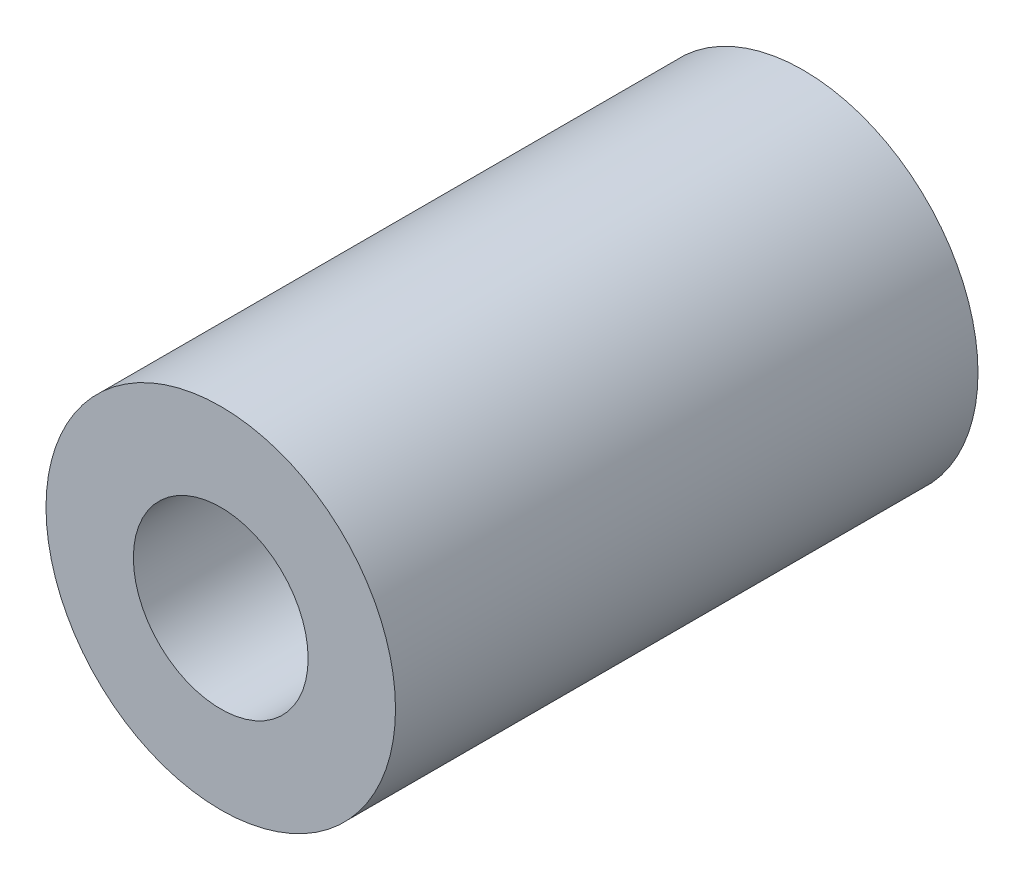
SolidWorks part; units mm, degrees
material "1060 Alloy"
ref_plane "Front Plane" through (0, 0, 0) normal (0, 0, 1) x (1, 0, 0)
ref_plane "Top Plane" through (0, 0, 0) normal (0, 1, 0) x (1, 0, 0)
ref_plane "Right Plane" through (0, 0, 0) normal (1, 0, 0) x (0, 0, -1)
sketch "Sketch1" plane through (0, 0, 0) normal (0, 0, 1) x (1, 0, 0)
  circle A0 centre (0, 0) radius 1.5
  circle A1 centre (0, 0) radius 3
  dimension "D1" = 3
  dimension "D2" = 6
extrude "Boss-Extrude1" add sketch "Sketch1" along normal blind 10
